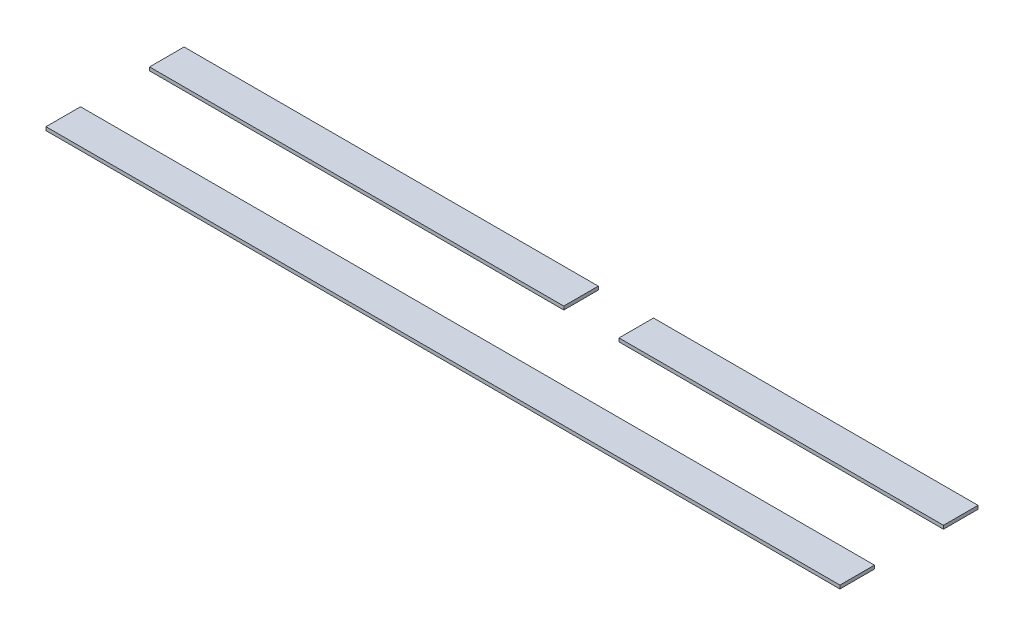
SolidWorks part; units mm, degrees
ref_plane "Front Plane" through (0, 0, 0) normal (0, 0, 1) x (1, 0, 0)
ref_plane "Top Plane" through (0, 0, 0) normal (0, 1, 0) x (1, 0, 0)
ref_plane "Right Plane" through (0, 0, 0) normal (1, 0, 0) x (0, 0, -1)
sketch "Sketch1" plane through (0, 0, 0) normal (0, 1, 0) x (1, 0, 0)
  line L1 (0, 0) -> (230, 0)
  line L2 (0, 0) -> (0, 10)
  line L3 (0, 10) -> (230, 10)
  line L4 (230, 0) -> (230, 10)
  line L5 (136, 30) -> (136, 40)
  line L6 (120, 30) -> (120, 40)
  line L7 (120, 40) -> (0, 40)
  line L8 (0, 40) -> (0, 30)
  line L10 (136, 40) -> (230, 40)
  line L11 (230, 40) -> (230, 30)
  line L12 (230, 30) -> (136, 30)
  line L15 (120, 30) -> (0, 30)
extrude "Boss-Extrude1" add sketch "Sketch1" along normal blind 1
